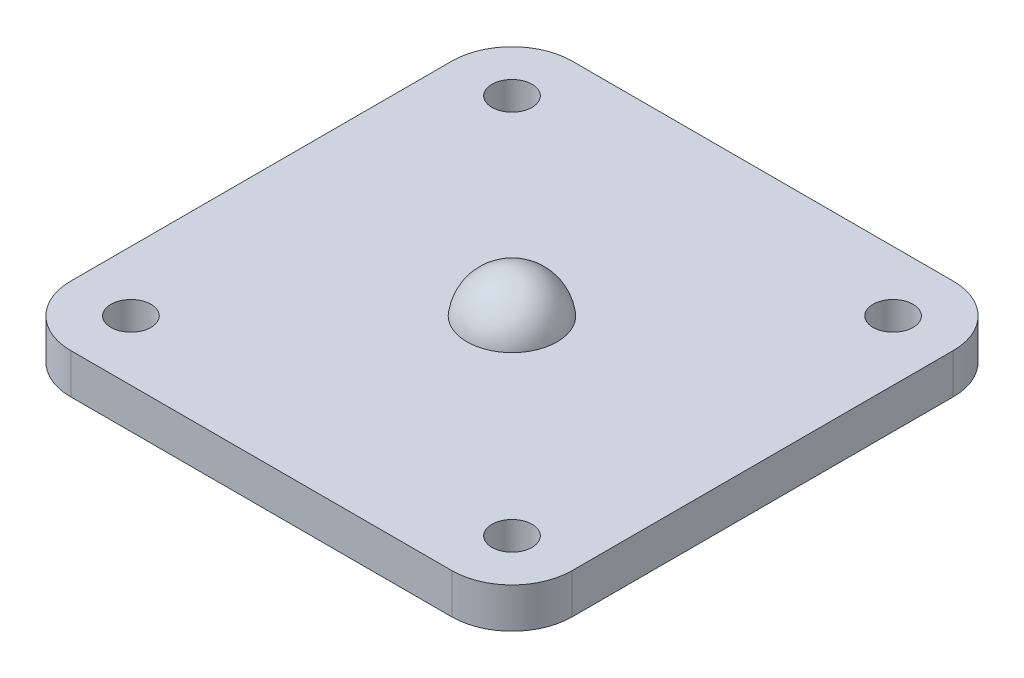
SolidWorks part; units mm, degrees
ref_plane "Front Plane" through (0, 0, 0) normal (0, 0, 1) x (1, 0, 0)
ref_plane "Top Plane" through (0, 0, 0) normal (0, 1, 0) x (1, 0, 0)
ref_plane "Right Plane" through (0, 0, 0) normal (1, 0, 0) x (0, 0, -1)
sketch "Sketch1" plane through (0, 0, 0) normal (0, 1, 0) x (1, 0, 0)
  line L1 (-12.5, -12.5) -> (12.5, -12.5)
  line L2 (-12.5, -12.5) -> (-12.5, 12.5)
  line L3 (-12.5, 12.5) -> (12.5, 12.5)
  line L4 (12.5, -12.5) -> (12.5, 12.5)
  line L5 (-12.5, -12.5) -> (12.5, 12.5) construction
  line L6 (-12.5, 12.5) -> (12.5, -12.5) construction
  point P0 (0, 0)
  dimension "D1" = 25
extrude "Boss-Extrude1" add sketch "Sketch1" along normal blind 2
fillet "Fillet1" radius 3 4 edges at (-12.5, 1, -12.5) (12.5, 1, -12.5) (-12.5, 1, 12.5) (12.5, 1, 12.5)
sketch "Sketch2" plane through (0, 2, 0) normal (0, 1, 0) x (1, 0, 0)
  circle A0 centre (-9.5, 9.5) radius 1
  circle A1 centre (9.5, 9.5) radius 1
  circle A2 centre (9.5, -9.5) radius 1
  circle A3 centre (-9.5, -9.5) radius 1
  arc A4 (9.5, -12.5) -> (12.5, -9.5) centre (9.5, -9.5) ccw construction
  arc A5 (-9.5, 12.5) -> (-12.5, 9.5) centre (-9.5, 9.5) ccw construction
  point P8 (0, 0)
  point P9 (0, 0)
  point P10 (0, 0)
  point P11 (0, 0)
  point P12 (0, 0)
  point P13 (0, 0)
  dimension "D1" = 2
extrude "Cut-Extrude1" cut sketch "Sketch2" against normal up to next
sketch "Sketch3" plane through (0, 0, 0) normal (0, 0, 1) x (1, 0, 0)
  line L0 (0, 2) -> (0, 4)
  line L1 (-9.5, 2) -> (9.5, 2) construction
  line L2 (2.25, 2) -> (0, 2)
  line L3 (0.1741, 4) -> (1.9339, 4) construction
  arc A1 (0, 4) -> (2.25, 2) centre (0, 1.7344) cw
  dimension "D1" = 2
  dimension "D2" = 2.25
revolve "Revolve1" add sketch "Sketch3" angle 360 about L0
